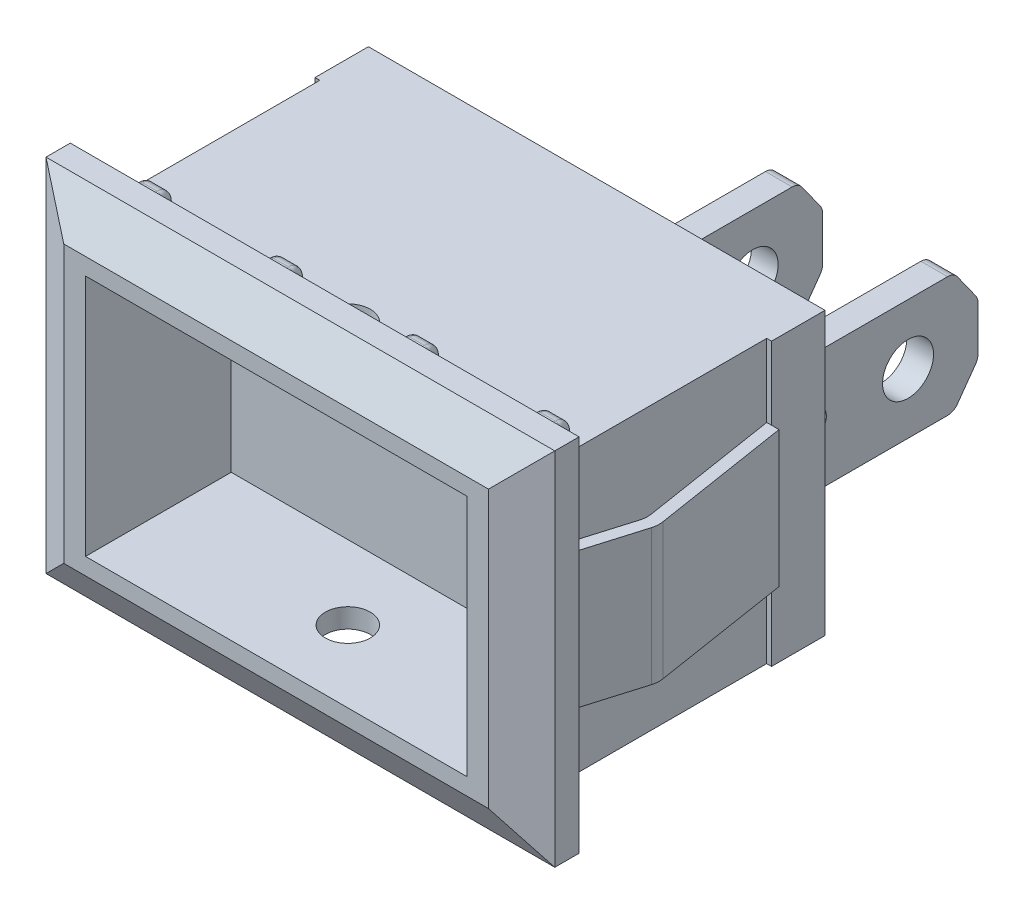
SolidWorks part; units mm, degrees
ref_plane "Ön Düzlem" through (0, 0, 0) normal (0, 0, 1) x (1, 0, 0)
ref_plane "Üst Düzlem" through (0, 0, 0) normal (0, 1, 0) x (1, 0, 0)
ref_plane "Sağ Düzlem" through (0, 0, 0) normal (1, 0, 0) x (0, 0, -1)
sketch "Çizim1" plane through (0, 0, 0) normal (0, 0, 1) x (1, 0, 0)
  line L1 (0, 0) -> (18.8, 0)
  line L2 (0, 0) -> (0, 11.6)
  line L3 (0, 11.6) -> (18.8, 11.6)
  line L4 (18.8, 0) -> (18.8, 11.6)
  dimension "D1" = 18.8
  dimension "D2" = 11.6
extrude "Yükseklik-Ekstrüzyon1" add sketch "Çizim1" along normal blind 2.2
sketch "Çizim2" plane through (0, 0, 2.2) normal (0, 0, 1) x (1, 0, 0)
  line L0 (18.8, 11.6) -> (0, 11.6) construction
  line L1 (0.2, 11.6) -> (18.6, 11.6)
  line L2 (0.2, 11.6) -> (0.2, 0)
  line L3 (0.2, 0) -> (18.6, 0)
  line L4 (18.6, 11.6) -> (18.6, 0)
  line L5 (0, 0) -> (18.8, 0) construction
  line L8 (0, 11.6) -> (0, 0) construction
  dimension "D1" = 18.4
  dimension "D2" = 0.2
extrude "Yükseklik-Ekstrüzyon2" add sketch "Çizim2" along normal blind 9
sketch "Çizim3" plane through (0, 0, 0) normal (0, 0, -1) x (-1, 0, 0)
  line L0 (0, 11.6) -> (0, 0) construction
  line L1 (-1.95, 7.7) -> (-1, 7.7)
  line L2 (-1.95, 7.7) -> (-1.95, 4)
  line L3 (-1.95, 4) -> (-1, 4)
  line L4 (-1, 7.7) -> (-1, 4)
  line L5 (0, 0) -> (-18.8, 0) construction
  line L7 (-2.95, 7.7) -> (-3.9, 7.7)
  line L8 (-2.95, 7.7) -> (-2.95, 4)
  line L9 (-2.95, 4) -> (-3.9, 4)
  line L10 (-3.9, 7.7) -> (-3.9, 4)
  dimension "D1" = 1
  dimension "D2" = 3.7
  dimension "D3" = 7.7
  dimension "D4" = 0.95
  dimension "D5" = 0.95
  dimension "D6" = 1
extrude "Yükseklik-Ekstrüzyon3" add sketch "Çizim3" along normal blind 1
sketch "Çizim4" plane through (0, 0, 0) normal (0, 0, -1) x (-1, 0, 0)
  line L0 (-2.95, 7.7) -> (-3.9, 7.7) construction
  line L5 (-9.35, 7.7) -> (-8.4, 7.7)
  line L6 (-9.35, 7.7) -> (-9.35, 4)
  line L7 (-9.35, 4) -> (-8.4, 4)
  line L8 (-8.4, 7.7) -> (-8.4, 4)
  line L9 (-3.9, 4) -> (-2.95, 4) construction
  line L10 (-3.9, 7.7) -> (-3.9, 4) construction
  line L11 (-10.45, 7.7) -> (-11.4, 7.7)
  line L12 (-10.45, 7.7) -> (-10.45, 4)
  line L13 (-10.45, 4) -> (-11.4, 4)
  line L14 (-11.4, 7.7) -> (-11.4, 4)
  line L20 (-14.8, 5.85) -> (-11.4, 5.85) construction
  line L21 (-13.1, 5.85) -> (-13.1, 11.6) construction
  line L22 (-18.8, 11.6) -> (0, 11.6) construction
  line L23 (-13.1, 11.6) -> (-13.1, 0) construction
  line L24 (0, 0) -> (-18.8, 0) construction
  line L25 (-14.8, 7.7) -> (-14.8, 4)
  line L26 (-15.75, 4) -> (-14.8, 4)
  line L27 (-15.75, 7.7) -> (-15.75, 4)
  line L28 (-15.75, 7.7) -> (-14.8, 7.7)
  line L29 (-17.8, 7.7) -> (-17.8, 4)
  line L30 (-16.85, 4) -> (-17.8, 4)
  line L31 (-16.85, 7.7) -> (-16.85, 4)
  line L32 (-16.85, 7.7) -> (-17.8, 7.7)
  dimension "D1" = 0.95
  dimension "D2" = 0
  dimension "D3" = 0
  dimension "D4" = 0.95
  dimension "D5" = 3
  dimension "D6" = 4.5
extrude "Yükseklik-Ekstrüzyon4" add sketch "Çizim4" along normal blind 1
sketch "Çizim5" plane through (0, 0, 0) normal (0, 0, -1) x (-1, 0, 0)
  line L0 (-15.75, 7.7) -> (-15.75, 4) construction
  line L2 (-16.85, 7.7) -> (-17.8, 7.7) construction
  line L4 (-16.85, 8.325) -> (-15.75, 8.325)
  line L5 (-16.85, 8.325) -> (-16.85, 3.375)
  line L6 (-16.85, 3.375) -> (-15.75, 3.375)
  line L7 (-15.75, 8.325) -> (-15.75, 3.375)
  line L8 (-16.85, 4) -> (-16.85, 7.7) construction
  line L9 (-16.85, 5.85) -> (-14.0588, 5.85) construction
  line L10 (-14.8, 5.85) -> (-11.4, 5.85) construction
  line L11 (-14.8, 4) -> (-14.8, 7.7) construction
  line L12 (-11.4, 7.7) -> (-11.4, 4) construction
  line L13 (-13.1, 5.85) -> (-13.1, 9.7451) construction
  line L14 (-9.35, 5.85) -> (-12.1412, 5.85) construction
  line L15 (-10.45, 8.325) -> (-10.45, 3.375)
  line L16 (-9.35, 3.375) -> (-10.45, 3.375)
  line L17 (-9.35, 8.325) -> (-9.35, 3.375)
  line L18 (-9.35, 8.325) -> (-10.45, 8.325)
  dimension "D1" = 0
  dimension "D2" = 0
  dimension "D3" = 4.95
  dimension "D4" = 0.625
extrude "Yükseklik-Ekstrüzyon5" add sketch "Çizim5" along normal blind 8.25
sketch "Çizim6" plane through (16.85, 0, 0) normal (1, 0, 0) x (0, 0, -1)
  line L0 (7.2551, 8.325) -> (8.25, 6.9308)
  line L1 (8.25, 8.325) -> (0, 8.325) construction
  line L2 (8.25, 8.325) -> (8.25, 3.375) construction
  line L3 (8.25, 5.85) -> (-14.1085, 5.85) construction
  line L4 (1, 6.3213) -> (1, 5.3787)
  line L5 (1, 7.7) -> (1, 4) construction
  line L6 (7.2551, 3.375) -> (8.25, 4.7692)
  line L7 (7.2551, 8.325) -> (8.25, 8.325)
  line L8 (8.25, 8.325) -> (8.25, 6.9308)
  line L9 (8.25, 3.375) -> (7.2551, 3.375)
  line L10 (8.25, 4.7692) -> (8.25, 3.375)
  circle A0 centre (5.3697, 5.85) radius 1.05
  arc A1 (1, 5.3787) -> (1, 6.3213) centre (1.3923, 5.85) ccw
  dimension "D1" = 2.1
extrude "Kes-Ekstrüzyon1" cut sketch "Çizim6" against normal blind 8.25
fillet "Radyus1" radius 0.5 8 edges at (9.9, 8.325, -7.2551) (9.9, 6.9308, -8.25) (9.9, 4.7692, -8.25) (9.9, 3.375, -7.2551) (16.3, 3.375, -7.2551) (16.3, 4.7692, -8.25) (16.3, 6.9308, -8.25) (16.3, 8.325, -7.2551)
sketch "Çizim7" plane through (0, 0, 11.2) normal (0, 0, 1) x (1, 0, 0)
  line L0 (9.4, 0) -> (9.4, 11.6) construction
  line L1 (0.2, 0) -> (18.6, 0) construction
  line L2 (18.6, 11.6) -> (0.2, 11.6) construction
  line L3 (18.6, 5.8) -> (0.2, 5.8) construction
  line L4 (18.6, 0) -> (18.6, 11.6) construction
  line L5 (0.2, 11.6) -> (0.2, 0) construction
  line L7 (19.875, 13.225) -> (-1.075, 13.225)
  line L8 (19.875, 13.225) -> (19.875, -1.625)
  line L9 (19.875, -1.625) -> (-1.075, -1.625)
  line L10 (-1.075, 13.225) -> (-1.075, -1.625)
  line L11 (19.875, 13.225) -> (-1.075, -1.625) construction
  line L12 (19.875, -1.625) -> (-1.075, 13.225) construction
  point P12 (9.4, 5.8)
  dimension "D1" = 20.95
  dimension "D2" = 14.85
extrude "Yükseklik-Ekstrüzyon6" add sketch "Çizim7" along normal blind 2
sketch "Çizim8" plane through (0, 13.225, 0) normal (0, 1, 0) x (1, 0, 0)
  line L0 (19.875, -12.2) -> (18.1429, -13.2)
  line L1 (19.875, -13.2) -> (19.875, -11.2) construction
  line L2 (19.875, -13.2) -> (-1.075, -13.2) construction
  line L3 (19.875, -12.2) -> (19.875, -13.2)
  line L4 (19.875, -13.2) -> (18.1429, -13.2)
  line L5 (9.4, -13.2) -> (9.4, -6.9876) construction
  line L6 (-1.075, -13.2) -> (0.6571, -13.2)
  line L7 (-1.075, -12.2) -> (-1.075, -13.2)
  line L8 (-1.075, -12.2) -> (0.6571, -13.2)
  dimension "D1" = 30
extrude "Kes-Ekstrüzyon2" cut sketch "Çizim8" against normal blind 19
sketch "Çizim9" plane through (-1.075, 0, 0) normal (-1, 0, 0) x (0, 0, 1)
  line L0 (13.2, 13.225) -> (12.2, 13.225)
  line L1 (12.2, 13.225) -> (13.2, 11.495)
  line L2 (13.2, 13.225) -> (13.2, -1.625) construction
  line L3 (13.2, 11.495) -> (13.2, 13.225)
  line L4 (13.2, 5.8) -> (15.0365, 5.8) construction
  line L5 (13.2, 0.105) -> (13.2, -1.625)
  line L6 (12.2, -1.625) -> (13.2, 0.105)
  line L7 (13.2, -1.625) -> (12.2, -1.625)
  dimension "D1" = 1.73
extrude "Kes-Ekstrüzyon3" cut sketch "Çizim9" against normal blind 23
sketch "Çizim10" plane through (0, 0, 13.2) normal (0, 0, 1) x (1, 0, 0)
  line L1 (1.5521, 10.8) -> (17.2521, 10.8)
  line L2 (1.5521, 10.8) -> (1.5521, 0.8)
  line L3 (1.5521, 0.8) -> (17.2521, 0.8)
  line L4 (17.2521, 10.8) -> (17.2521, 0.8)
  line L8 (18.1429, 0.105) -> (0.6571, 0.105) construction
  line L9 (0.6571, 11.495) -> (0.6571, 0.105) construction
  dimension "D1" = 15.7
  dimension "D2" = 10
  dimension "D3" = 0.695
  dimension "D4" = 0.895
extrude "Kes-Ekstrüzyon5" cut sketch "Çizim10" against normal blind 6
sketch "Çizim11" plane through (0, 11.6, 0) normal (0, 1, 0) x (1, 0, 0)
  line L0 (18.6, -11.2) -> (0.2, -11.2) construction
  line L1 (1.7, -11.2) -> (0.7, -11.2)
  line L2 (1.7, -11.2) -> (1.7, -9.7)
  line L3 (1.7, -9.7) -> (0.7, -9.7)
  line L4 (0.7, -11.2) -> (0.7, -9.7)
  line L5 (0.2, -11.2) -> (0.2, -2.2) construction
  line L6 (7.1, -11.2) -> (6.1, -11.2)
  line L7 (7.1, -11.2) -> (7.1, -9.7)
  line L8 (7.1, -9.7) -> (6.1, -9.7)
  line L9 (6.1, -11.2) -> (6.1, -9.7)
  line L10 (9.4, -11.2) -> (9.4, -4.6824) construction
  line L11 (12.7, -11.2) -> (12.7, -9.7)
  line L12 (11.7, -9.7) -> (12.7, -9.7)
  line L13 (11.7, -11.2) -> (11.7, -9.7)
  line L14 (11.7, -11.2) -> (12.7, -11.2)
  line L15 (18.1, -11.2) -> (18.1, -9.7)
  line L16 (17.1, -9.7) -> (18.1, -9.7)
  line L17 (17.1, -11.2) -> (17.1, -9.7)
  line L18 (17.1, -11.2) -> (18.1, -11.2)
  dimension "D1" = 1
  dimension "D2" = 1
  dimension "D3" = 4.4
  dimension "D4" = 1.5
  dimension "D5" = 1.5
  dimension "D6" = 0.5
extrude "Yükseklik-Ekstrüzyon7" add sketch "Çizim11" along normal blind 0.7
fillet "Radyus2" radius 0.5 4 edges at (17.6, 12.3, 9.7) (12.2, 12.3, 9.7) (6.6, 12.3, 9.7) (1.2, 12.3, 9.7)
fillet "Radyus3" radius 0.2 24 edges at (0.7, 11.7, 9.7) (0.7, 12.1536, 9.8464) (1.7, 11.7, 9.7) (1.7, 12.1536, 9.8464) (7.1, 11.7, 9.7) (7.1, 12.1536, 9.8464) (6.1, 11.7, 9.7) (6.1, 12.1536, 9.8464) (12.7, 11.7, 9.7) (12.7, 12.1536, 9.8464) (11.7, 11.7, 9.7) (11.7, 12.1536, 9.8464) (17.1, 11.7, 9.7) (17.1, 12.1536, 9.8464) (18.1, 11.7, 9.7) (18.1, 12.1536, 9.8464) (0.7, 12.3, 10.7) (1.7, 12.3, 10.7) (7.1, 12.3, 10.7) (6.1, 12.3, 10.7) (12.7, 12.3, 10.7) (11.7, 12.3, 10.7) (17.1, 12.3, 10.7) (18.1, 12.3, 10.7)
sketch "Çizim13" plane through (0, 0, 0) normal (0, -1, 0) x (1, 0, 0)
  line L0 (1.7, 9.7) -> (0.7, 9.7)
  line L1 (1.7, 9.7) -> (1.7, 11.2)
  line L2 (1.7, 11.2) -> (0.7, 11.2)
  line L3 (0.7, 9.7) -> (0.7, 11.2)
  line L4 (7.1, 9.7) -> (6.1, 9.7)
  line L5 (7.1, 9.7) -> (7.1, 11.2)
  line L6 (7.1, 11.2) -> (6.1, 11.2)
  line L7 (6.1, 9.7) -> (6.1, 11.2)
  line L8 (9.4, 8.2899) -> (9.4, 14.8075) construction
  line L9 (12.7, 9.7) -> (12.7, 11.2)
  line L10 (11.7, 11.2) -> (12.7, 11.2)
  line L11 (11.7, 9.7) -> (11.7, 11.2)
  line L12 (11.7, 9.7) -> (12.7, 9.7)
  line L13 (18.1, 9.7) -> (18.1, 11.2)
  line L14 (17.1, 11.2) -> (18.1, 11.2)
  line L15 (17.1, 9.7) -> (17.1, 11.2)
  line L16 (17.1, 9.7) -> (18.1, 9.7)
  line L17 (0.2, 11.2) -> (18.6, 11.2) construction
  line L18 (18.6, 11.2) -> (18.6, 2.2) construction
  line L19 (0.2, 11.2) -> (0.2, 2.2) construction
  dimension "D1" = 1
  dimension "D2" = 1
  dimension "D3" = 4.4
  dimension "D4" = 1.5
  dimension "D5" = 1.5
  dimension "D6" = 0.5
  dimension "D7" = 0.5
extrude "Yükseklik-Ekstrüzyon8" add sketch "Çizim13" along normal blind 0.7
fillet "Radyus4" radius 0.5 4 edges at (17.6, -0.7, 9.7) (12.2, -0.7, 9.7) (6.6, -0.7, 9.7) (1.2, -0.7, 9.7)
fillet "Radyus5" radius 0.2 24 edges at (18.1, -0.1, 9.7) (18.1, -0.5536, 9.8464) (17.1, -0.1, 9.7) (17.1, -0.5536, 9.8464) (12.7, -0.1, 9.7) (12.7, -0.5536, 9.8464) (11.7, -0.1, 9.7) (11.7, -0.5536, 9.8464) (6.1, -0.1, 9.7) (6.1, -0.5536, 9.8464) (7.1, -0.1, 9.7) (7.1, -0.5536, 9.8464) (1.7, -0.1, 9.7) (1.7, -0.5536, 9.8464) (0.7, -0.1, 9.7) (0.7, -0.5536, 9.8464) (18.1, -0.7, 10.7) (17.1, -0.7, 10.7) (12.7, -0.7, 10.7) (11.7, -0.7, 10.7) (6.1, -0.7, 10.7) (7.1, -0.7, 10.7) (1.7, -0.7, 10.7) (0.7, -0.7, 10.7)
ref_plane "Düzlem1" through (0, 5.8, 0) normal (0, 1, 0) x (1, 0, 0)
sketch "Çizim14" plane through (0, 5.8, 0) normal (0, 1, 0) x (1, 0, 0)
  line L0 (19.1062, -2.2) -> (20.0403, -8.1079)
  line L1 (20.0403, -8.1079) -> (19.1216, -11.2)
  line L2 (18.8, -2.2) -> (18.6, -2.2) construction
  line L3 (18.6, -2.2) -> (19.5288, -8.0741)
  line L4 (19.875, -11.2) -> (-1.075, -11.2) construction
  line L5 (19.5288, -8.0741) -> (18.6, -11.2)
  line L6 (19.1062, -2.2) -> (18.6, -2.2)
  line L7 (19.1216, -11.2) -> (18.6, -11.2)
  line L8 (18.6, -11.2) -> (18.6, -2.2) construction
  dimension "D1" = 0.5
  dimension "D2" = 0.5
  dimension "D3" = 0.9288
  dimension "D4" = 3.1259
extrude "Yükseklik-Ekstrüzyon9" add sketch "Çizim14" along normal blind 2.8 and the other way blind 2.8
fillet "Radyus6" radius 1 2 edges at (20.0403, 5.8, 8.1079) (19.5288, 5.8, 8.0741)
sketch "Çizim15" plane through (0, 5.8, 0) normal (0, 1, 0) x (1, 0, 0)
  line L0 (0.2, -11.2) -> (-0.73, -8.07)
  line L1 (-0.73, -8.07) -> (0.7353, -2.2)
  line L2 (-0.3216, -11.2) -> (-1.2482, -8.0814)
  line L3 (-1.2482, -8.0814) -> (0.22, -2.2)
  line L4 (0.2, -11.2) -> (-0.3216, -11.2)
  line L5 (0.7353, -2.2) -> (0.22, -2.2)
  line L6 (19.875, -11.2) -> (-1.075, -11.2) construction
  line L7 (0.2, -2.2) -> (0, -2.2) construction
  line L8 (0, -2.2) -> (0, 0) construction
  line L9 (0.2, -11.2) -> (0.2, -2.2) construction
  dimension "D1" = 0.5
  dimension "D2" = 0.5
  dimension "D3" = 0.22
  dimension "D4" = 0.93
  dimension "D5" = 3.13
extrude "Yükseklik-Ekstrüzyon10" add sketch "Çizim15" along normal blind 2.8 and the other way blind 2.8
fillet "Radyus7" radius 1 2 edges at (-0.73, 5.8, 8.07) (-1.2482, 5.8, 8.0814)
sketch "Çizim17" plane through (0, 11.6, 0) normal (0, 1, 0) x (1, 0, 0)
  line L0 (9.4, -12.2) -> (9.4, -2.6371) construction
  line L1 (19.875, -12.2) -> (-1.075, -12.2) construction
  circle A0 centre (9.4, -10.2472) radius 0.925
  dimension "D1" = 1.85
extrude "Kes-Ekstrüzyon7" cut sketch "Çizim17" against normal blind 20
